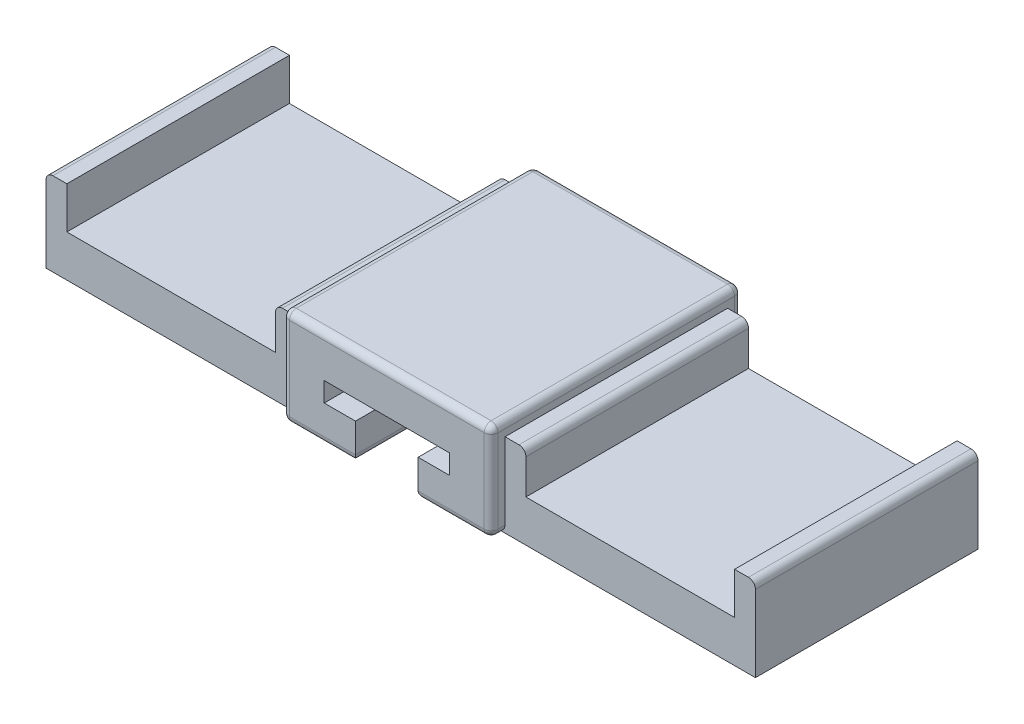
SolidWorks part; units mm, degrees
ref_plane "Front Plane" through (0, 0, 0) normal (0, 0, 1) x (1, 0, 0)
ref_plane "Top Plane" through (0, 0, 0) normal (0, 1, 0) x (1, 0, 0)
ref_plane "Right Plane" through (0, 0, 0) normal (1, 0, 0) x (0, 0, -1)
sketch "Sketch1" plane through (0, 0, 0) normal (0, 1, 0) x (1, 0, 0)
  line L1 (-7.5, -9) -> (7.5, -9)
  line L2 (-7.5, -9) -> (-7.5, 9)
  line L3 (-7.5, 9) -> (7.5, 9)
  line L4 (7.5, -9) -> (7.5, 9)
  line L5 (-7.5, -9) -> (7.5, 9) construction
  line L6 (-7.5, 9) -> (7.5, -9) construction
  point P0 (0, 0)
  dimension "D1" = 18
  dimension "D2" = 15
extrude "Boss-Extrude1" add sketch "Sketch1" along normal blind 7
sketch "Sketch2" plane through (0, 0, 9) normal (0, 0, 1) x (1, 0, 0)
  line L0 (-4.5, 0) -> (4.5, 0)
  line L1 (-7.5, 0) -> (7.5, 0) construction
  line L2 (4.5, 0) -> (4.5, 4)
  line L3 (4.5, 4) -> (-4.5, 4)
  line L4 (-4.5, 4) -> (-4.5, 0)
  line L5 (-4.5, 2.6) -> (4.5, 2.6)
  line L6 (-2.25, 2.6) -> (-2.25, 0)
  line L7 (0, 0) -> (0, 7) construction
  line L8 (-7.5, 7) -> (7.5, 7) construction
  line L9 (2.25, 2.6) -> (2.25, 0)
  line L10 (-0.6, 0) -> (-0.6, 5)
  line L11 (-0.6, 5) -> (0.6, 5)
  line L12 (0.6, 5) -> (0.6, 0)
  line L13 (1.1, 2.6) -> (1.1, 0)
  line L14 (-1.1, 2.6) -> (-1.1, 0)
  point P6 (0, 0)
  dimension "D1" = 4
  dimension "D2" = 1.4
  dimension "D3" = 4.5
  dimension "D4" = 1.2
  dimension "0.5" = 0.5
  dimension "D6" = 9
extrude "Cut-Extrude1" cut sketch "Sketch2" against normal blind 16.2 contours L5 L10 L3 L4 | L3 L12 L5 L2 | L5 L7 L3 L10 | L7 L5 L12 L3 | L14 L5 L6 L0 | L5 L14 L4 L10 | L4 L7 L5 L10 | L7 L0 L12 L5 | L13 L5 L12 L0 | L5 L13 L4 L9
sketch "Sketch8" plane through (0, 0, 9) normal (0, 0, 1) x (1, 0, 0)
  line L0 (-1.1, 2.6) -> (-0.6, 2.6)
  line L1 (-0.6, 2.6) -> (-0.6, 0)
  line L2 (-0.6, 0) -> (-1.1, 0)
  line L3 (-1.1, 0) -> (-1.1, 2.6)
  line L4 (0.6, 2.6) -> (1.1, 2.6)
  line L5 (1.1, 2.6) -> (1.1, 0)
  line L6 (1.1, 0) -> (0.6, 0)
  line L7 (0.6, 0) -> (0.6, 2.6)
sketch "Sketch9" plane through (-7.5, 0, 0) normal (-1, 0, 0) x (0, 0, 1)
  line L0 (-8, 0) -> (-8, 6)
  line L1 (9, 0) -> (-9, 0) construction
  line L2 (-8, 6) -> (8, 6)
  line L3 (8, 6) -> (8, 0)
  line L4 (-9, 0) -> (9, 0) construction
  line L5 (8, 0) -> (-8, 0)
  line L6 (-0.3093, 0) -> (0, 0) construction
  line L7 (0, 0) -> (0, 6) construction
  dimension "D1" = 16
  dimension "D2" = 6
extrude "Boss-Extrude2" add sketch "Sketch9" along normal blind 18
sketch "Sketch12" plane through (0, 0, 8) normal (0, 0, 1) x (1, 0, 0)
  line L0 (-16.5, 0) -> (-16.5, 6) construction
  line L1 (-25.5, 0) -> (-7.5, 0) construction
  line L2 (-25.5, 6) -> (-7.5, 6) construction
  dimension "D1" = 16.5
sketch "Sketch13" plane through (7.5, 0, 0) normal (1, 0, 0) x (0, 0, -1)
  line L0 (-8, 0) -> (-8, 6)
  line L1 (-8, 0) -> (-8, 6) construction
  line L2 (-8, 6) -> (8, 6)
  line L3 (8, 6) -> (8, 0)
  line L4 (9, 0) -> (-9, 0) construction
  line L5 (8, 0) -> (-8, 0)
  line L6 (0, 0) -> (0, 7) construction
  line L7 (-9, 0) -> (9, 0) construction
  line L8 (-9, 7) -> (9, 7) construction
  dimension "D2" = 6
extrude "Boss-Extrude3" add sketch "Sketch13" along normal blind 18
sketch "Sketch14" plane through (0, 0, 9) normal (0, 0, 1) x (1, 0, 0)
  line L0 (0, 0) -> (0, 7) construction
  line L1 (-7.5, 7) -> (7.5, 7) construction
  line L3 (25.5, 0) -> (7.5, 0) construction
  line L7 (16.5, 0) -> (16.5, 0.2814) construction
  line L12 (16.5, 0) -> (16.5, 6) construction
  line L13 (25.5, 6) -> (7.5, 6) construction
  line L17 (9, 6) -> (9, 3)
  line L18 (9, 3) -> (24, 3)
  line L19 (24, 3) -> (24, 6)
  line L20 (24, 6) -> (9, 6)
  line L23 (-24, 3) -> (-24, 6)
  line L24 (-9, 3) -> (-24, 3)
  line L25 (-9, 6) -> (-9, 3)
  line L30 (-24, 6) -> (-9, 6)
  dimension "D1" = 15
  dimension "D2" = 3
extrude "Cut-Extrude5" cut sketch "Sketch14" against normal blind 32.55
fillet "Fillet1" radius 0.5 21 edges at (0, 0, -9) (0, 7, -9) (7.5, 0, -8.5) (-7.5, 0, -8.5) (-7.5, 0, 8.5) (7.5, 0, 8.5) (7.5, 7, 0) (25.5, 6, 0) (-25.5, 6, 0) (-7.5, 7, 0) (-7.5, 3.5, 9) (7.5, 3.5, 9) (4.875, 0, 9) (2.25, 0, 0.9) (-2.25, 0, 0.9) (-4.875, 0, 9) (0, 7, 9) (7.5, 3.5, -9) (-7.5, 3.5, -9) (-9, 6, 0) (9, 6, 0)
